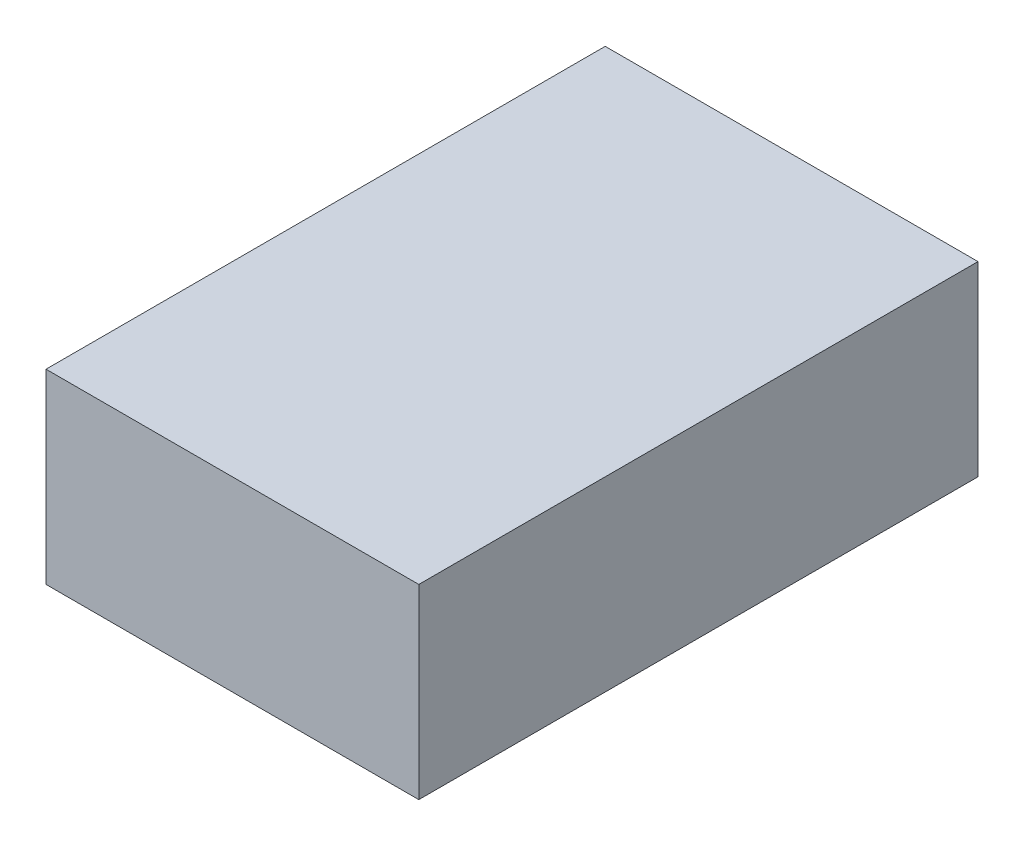
SolidWorks part; units mm, degrees
ref_plane "Alzado" through (0, 0, 0) normal (0, 0, 1) x (1, 0, 0)
ref_plane "Planta" through (0, 0, 0) normal (0, 1, 0) x (1, 0, 0)
ref_plane "Vista lateral" through (0, 0, 0) normal (1, 0, 0) x (0, 0, -1)
sketch "Sketch1" plane through (0, 0, 0) normal (0, 0, 1) x (1, 0, 0)
  line L1 (-100, 50) -> (100, 50)
  line L2 (-100, 50) -> (-100, -50)
  line L3 (-100, -50) -> (100, -50)
  line L4 (100, 50) -> (100, -50)
  line L5 (-100, 50) -> (100, -50) construction
  line L6 (-100, -50) -> (100, 50) construction
  point P0 (0, 0)
  dimension "D1" = 200
  dimension "D2" = 100
extrude "Boss-Extrude1" add sketch "Sketch1" along normal blind 300
